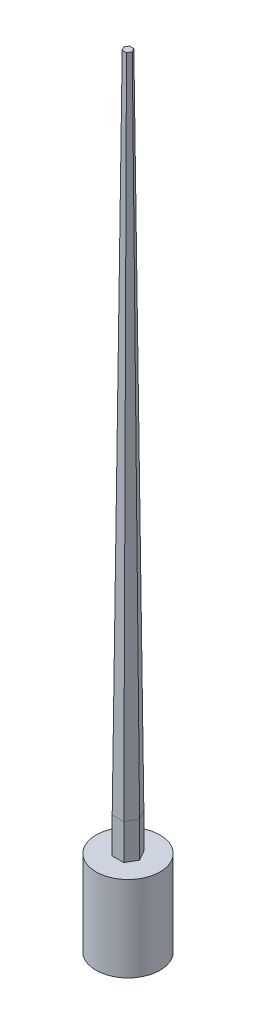
SolidWorks part; units mm, degrees
ref_plane "Alzado" through (0, 0, 0) normal (0, 0, 1) x (1, 0, 0)
ref_plane "Planta" through (0, 0, 0) normal (0, 1, 0) x (1, 0, 0)
ref_plane "Vista lateral" through (0, 0, 0) normal (1, 0, 0) x (0, 0, -1)
sketch "Croquis1" plane through (0, 0, 0) normal (0, 1, 0) x (1, 0, 0)
  line L1 (181.8653, 0) -> (90.9327, 157.5)
  line L2 (90.9327, 157.5) -> (-90.9327, 157.5)
  line L3 (-90.9327, 157.5) -> (-181.8653, 0)
  line L4 (-181.8653, 0) -> (-90.9327, -157.5)
  line L5 (-90.9327, -157.5) -> (90.9327, -157.5)
  line L6 (90.9327, -157.5) -> (181.8653, 0)
  circle A0 centre (0, 0) radius 157.5 construction
  dimension "D1" = 315
extrude "Saliente-Extruir1" add sketch "Croquis1" along normal blind 11000 draft 0.55
ref_plane "Plano1" through (0, 0, 0) normal (1, 0, 0) x (0, 0, -1)
ref_plane "Plano2" through (0, 0, 0) normal (0, 0, 1) x (1, 0, 0)
sketch "Croquis2" plane through (0, 0, 0) normal (0, -1, 0) x (1, 0, 0)
  circle A0 centre (0, 0) radius 450
  dimension "D1" = 900
extrude "Saliente-Extruir2" add sketch "Croquis2" against normal blind 1700
sketch "Croquis3" plane through (0, 1700, 0) normal (0, 1, 0) x (1, 0, 0)
  line L0 (163.0214, 0) -> (81.5107, -141.1807)
  line L1 (81.5107, -141.1807) -> (-81.5107, -141.1807)
  line L2 (-81.5107, -141.1807) -> (-163.0214, 0)
  line L3 (-168.2452, 0) -> (168.2452, 0) construction
  line L4 (-163.0214, 0) -> (-81.5107, 141.1807)
  line L5 (-81.5107, 141.1807) -> (81.5107, 141.1807)
  line L6 (81.5107, 141.1807) -> (163.0214, 0)
  circle A0 centre (0, 0) radius 466.8929
extrude "Cortar-Extruir1" cut sketch "Croquis3" against normal blind 500
